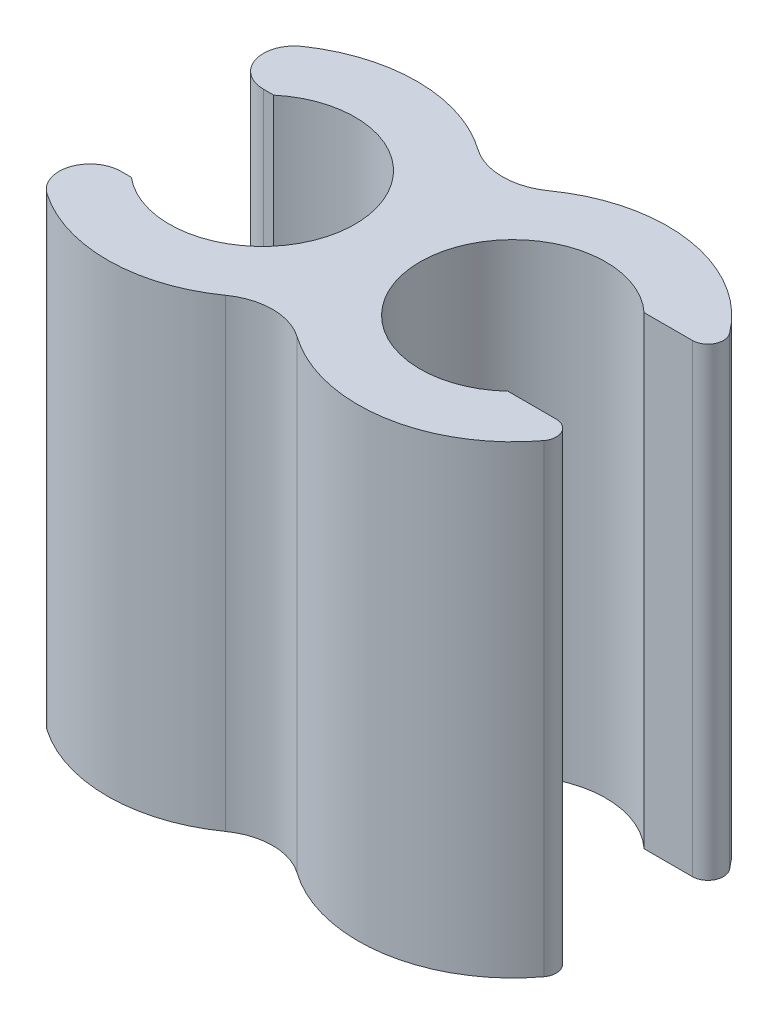
SolidWorks part; units mm, degrees
ref_plane "Front Plane" through (0, 0, 0) normal (0, 0, 1) x (1, 0, 0)
ref_plane "Top Plane" through (0, 0, 0) normal (0, 1, 0) x (1, 0, 0)
ref_plane "Right Plane" through (0, 0, 0) normal (1, 0, 0) x (0, 0, -1)
sketch "Sketch1" plane through (0, 0, 0) normal (0, 1, 0) x (1, 0, 0)
  circle A0 centre (0, 0) radius 5
  circle A1 centre (0, 0) radius 3
  dimension "D1" = 10
  dimension "D2" = 6
extrude "Boss-Extrude1" add sketch "Sketch1" along normal blind 15
sketch "Sketch2" plane through (0, 15, 0) normal (0, 1, 0) x (1, 0, 0)
  circle A0 centre (8.1, -0.0023) radius 3
  circle A1 centre (8.1, -0.0023) radius 5
  dimension "D1" = 10
  dimension "D2" = 6
extrude "Boss-Extrude2" add sketch "Sketch2" against normal blind 15
fillet "Fillet1" radius 2 2 edges at (4.0492, 7.5, 2.9333) (4.0509, 7.5, -2.931)
sketch "Sketch3" plane through (0, 0, 0) normal (0, -1, 0) x (1, 0, 0)
  line L1 (-7.3092, 2.3) -> (0, 2.3)
  line L2 (-7.3092, 2.3) -> (-7.3092, -2.3)
  line L3 (-7.3092, -2.3) -> (0, -2.3)
  line L4 (0, 2.3) -> (0, -2.3)
  circle A0 centre (0, 0) radius 3 construction
  dimension "D2" = 2.3
  dimension "D1" = 2.3
extrude "Cut-Extrude1" cut sketch "Sketch3" against normal blind 15
fillet "Fillet2" radius 1 2 edges at (-4.4396, 7.5, 2.3) (-4.4396, 7.5, -2.3)
sketch "Sketch4" plane through (0, 15, 0) normal (0, 1, 0) x (1, 0, 0)
  line L1 (8.5236, 2.1977) -> (15.41, 2.1977)
  line L2 (8.5236, 2.1977) -> (8.5236, -2.2023)
  line L3 (8.5236, -2.2023) -> (15.41, -2.2023)
  line L4 (15.41, 2.1977) -> (15.41, -2.2023)
  arc A0 (5.206, -4.0796) -> (5.2083, 4.0766) centre (8.1, -0.0023) ccw construction
  dimension "D1" = 2.2
  dimension "D2" = 2.2
extrude "Cut-Extrude2" cut sketch "Sketch4" against normal blind 15
fillet "Fillet3" radius 0.5 2 edges at (12.59, 7.5, 2.2023) (12.59, 7.5, -2.1977)
